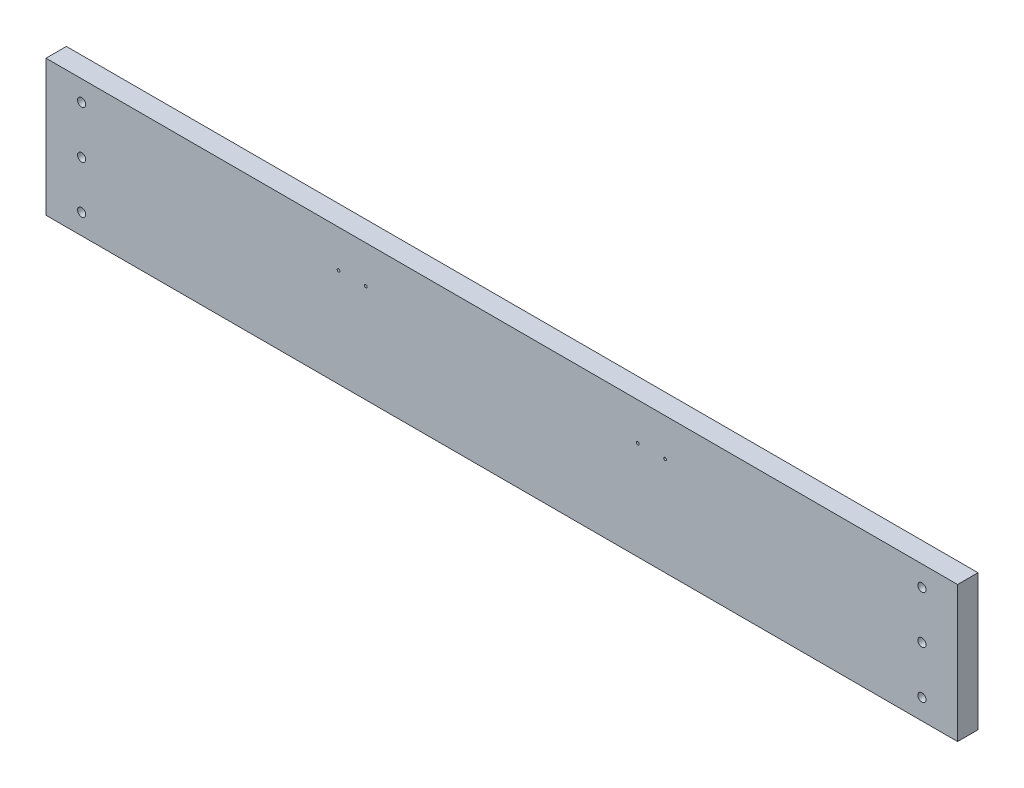
SolidWorks part; units mm, degrees
ref_plane "Front Plane" through (0, 0, 0) normal (0, 0, 1) x (1, 0, 0)
ref_plane "Top Plane" through (0, 0, 0) normal (0, 1, 0) x (1, 0, 0)
ref_plane "Right Plane" through (0, 0, 0) normal (1, 0, 0) x (0, 0, -1)
sketch "Sketch1" plane through (0, 0, 0) normal (0, 1, 0) x (1, 0, 0)
  line L0 (0, 0) -> (812.8, 0)
  line L4 (0, 0) -> (-19.05, 0)
  line L7 (812.8, 0) -> (831.85, 0)
  line L13 (812.8, 0) -> (812.8, -19.05)
  line L14 (812.8, -19.05) -> (0, -19.05)
  line L15 (0, -19.05) -> (0, 0)
  line L18 (-19.05, 0) -> (-19.05, -19.05)
  line L19 (-19.05, -19.05) -> (0, -19.05)
  line L20 (831.85, 0) -> (831.85, -19.05)
  line L21 (831.85, -19.05) -> (812.8, -19.05)
  dimension "D3" = 19.05
  dimension "D6" = 19.05
extrude "Boss-Extrude2" add sketch "Sketch1" along normal blind 127 contours L15 L14 L13 L0 | L21 L20 L7 L13 | L18 L19 L15 L4
sketch "Sketch2" plane through (0, 0, 0) normal (0, 0, -1) x (-1, 0, 0)
  line L0 (19.05, 127) -> (-831.85, 127) construction
  line L1 (-831.85, 127) -> (-831.85, 0) construction
  line L3 (-406.4, 127) -> (-406.4, 0)
  line L4 (19.05, 0) -> (-831.85, 0) construction
  circle A0 centre (-798.576, 107.95) radius 3.81
  circle A1 centre (-798.576, 63.5) radius 3.81
  circle A2 centre (-798.576, 19.05) radius 3.81
  circle A3 centre (-14.224, 19.05) radius 3.81
  circle A4 centre (-14.224, 63.5) radius 3.81
  circle A5 centre (-14.224, 107.95) radius 3.81
  dimension "D2" = 7.62
  dimension "D5" = 7.62
  dimension "D8" = 7.62
  dimension "D1" = 19.05
  dimension "D3" = 33.274
  dimension "D4" = 33.274
  dimension "D6" = 44.45
  dimension "D7" = 44.45
  dimension "D9" = 33.274
extrude "Cut-Extrude1" cut sketch "Sketch2" against normal blind 19.05 contours A5 | A4 | A3 | A2 | A0 | A1
sketch "Sketch3" plane through (0, 0, 0) normal (0, 0, -1) x (-1, 0, 0)
  line L0 (-831.85, 127) -> (-831.85, 0) construction
  line L1 (19.05, 127) -> (19.05, 0) construction
  line L2 (19.05, 0) -> (-831.85, 0) construction
  line L3 (-701.548, 28.702) -> (-701.548, 0)
  line L4 (-663.448, 28.702) -> (-663.448, 0)
  line L5 (-387.35, 28.702) -> (-387.35, 0)
  line L6 (-425.45, 28.702) -> (-425.45, 0)
  line L7 (-111.252, 28.702) -> (-111.252, 0)
  line L8 (-149.352, 28.702) -> (-149.352, 0)
  circle A0 centre (-682.498, 28.702) radius 19.05
  circle A1 centre (-406.4, 28.702) radius 19.05
  circle A2 centre (-130.302, 28.702) radius 19.05
  line M7 (-831.85, 0) -> (19.05, 0)
  dimension "D1" = 38.1
  dimension "D2" = 38.1
  dimension "D3" = 38.1
  dimension "D4" = 149.352
  dimension "D5" = 276.098
  dimension "D6" = 276.098
  dimension "D7" = 149.352
  dimension "D8" = 28.702
  dimension "D9" = 28.702
extrude "Cut-Extrude2" cut sketch "Sketch3" against normal blind 5.08 contours A0 L3 L4 M7 | A0 | A1 | A1 L6 L5 M7 | A2 L8 L7 M7 | A2
sketch "Sketch4" plane through (0, 0, 0) normal (0, 0, -1) x (-1, 0, 0)
  line L0 (-406.4, 127) -> (-406.4, 0)
  line L1 (19.05, 127) -> (-831.85, 127) construction
  line L2 (-831.85, 127) -> (-831.85, 0) construction
  circle A0 centre (-558.8, 91.948) radius 1.27
  circle A1 centre (-533.4, 91.948) radius 1.27
  circle A2 centre (-279.4, 91.948) radius 1.27
  circle A3 centre (-254, 91.948) radius 1.27
  dimension "D1" = 2.54
  dimension "D2" = 2.54
  dimension "D4" = 298.45
  dimension "D5" = 35.052
  dimension "D6" = 35.052
  dimension "D3" = 273.05
extrude "Cut-Extrude3" cut sketch "Sketch4" against normal blind 19.05 contours A0 | A1 | A2 | A3
